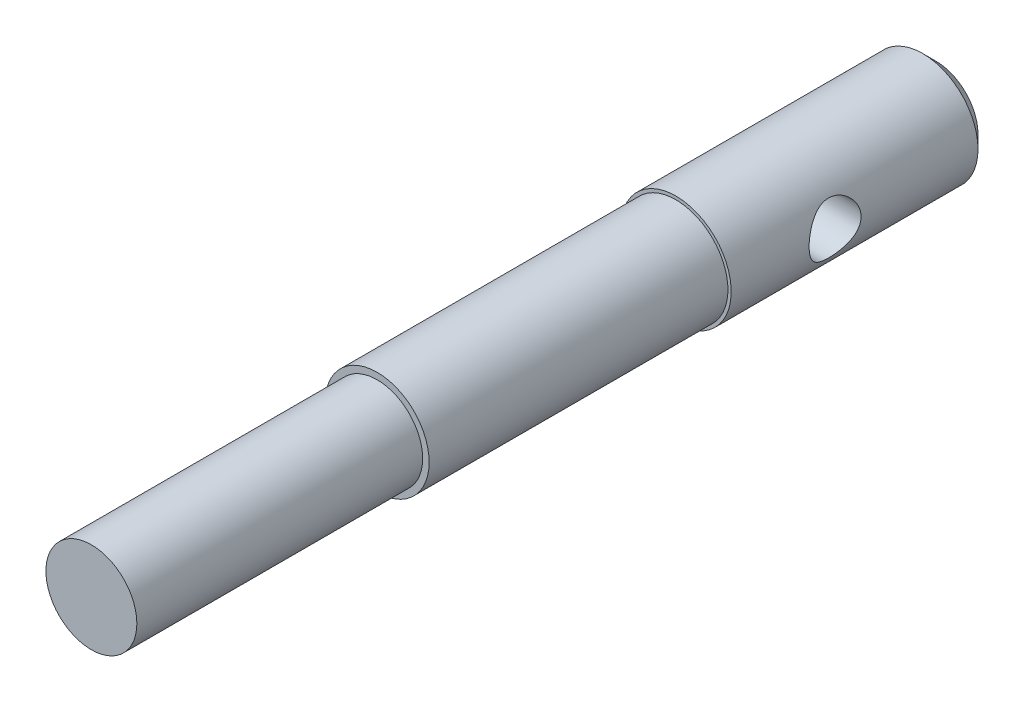
SolidWorks part; units mm, degrees
material "1060 Legierung"
ref_plane "Ebene vorne" through (0, 0, 0) normal (0, 0, 1) x (1, 0, 0)
ref_plane "Ebene oben" through (0, 0, 0) normal (0, 1, 0) x (1, 0, 0)
ref_plane "Ebene rechts" through (0, 0, 0) normal (1, 0, 0) x (0, 0, -1)
sketch "Skizze1" plane through (0, 0, 0) normal (0, 0, 1) x (1, 0, 0)
  circle A0 centre (0, 0) radius 4
  dimension "D1" = 8
extrude "Aufsatz-Linear austragen1" add sketch "Skizze1" along normal blind 65
sketch "Skizze2" plane through (0, 0, 0) normal (0, 0, -1) x (-1, 0, 0)
  circle A0 centre (0, 0) radius 4.25
  dimension "D1" = 8.5
extrude "Aufsatz-Linear austragen2" add sketch "Skizze2" against normal blind 20
sketch "Skizze3" plane through (0, 0, 0) normal (1, 0, 0) x (0, 0, -1)
  circle A0 centre (-12, 0) radius 2
  dimension "D1" = 4
  dimension "D2" = 12
extrude "Schnitt-Linear austragen1" cut sketch "Skizze3" against normal through all both and the other way through all
chamfer "Fase1" distance 1 angle 45 1 edges at (-4.25, 0, 0)
sketch "Skizze4" plane through (0, 0, 65) normal (0, 0, 1) x (1, 0, 0)
  circle A0 centre (0, 0) radius 4
  circle A1 centre (0, 0) radius 3.5
  dimension "D1" = 7
  dimension "D2" = 8
extrude "Schnitt-Linear austragen2" cut sketch "Skizze4" against normal blind 22
